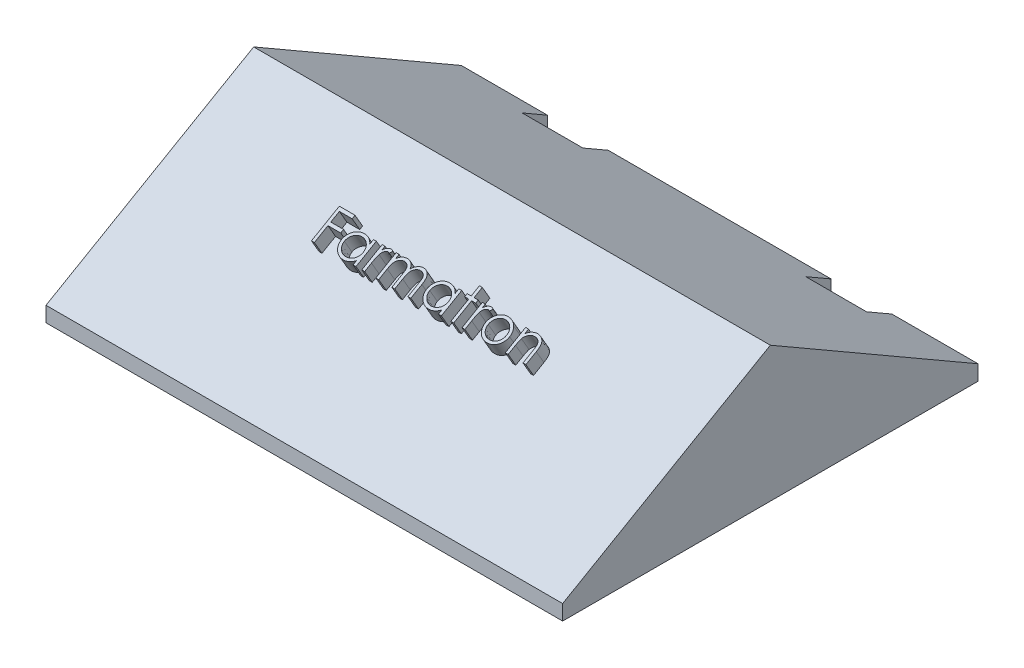
SolidWorks part; units mm, degrees
ref_plane "Front" through (0, 0, 0) normal (0, 0, 1) x (1, 0, 0)
ref_plane "Top" through (0, 0, 0) normal (0, 1, 0) x (1, 0, 0)
ref_plane "Right" through (0, 0, 0) normal (1, 0, 0) x (0, 0, -1)
sketch "Sketch1" plane through (0, 0, 0) normal (0, 1, 0) x (1, 0, 0)
  line L1 (-51, -41) -> (51, -41)
  line L2 (-51, -41) -> (-51, 41)
  line L3 (-51, 41) -> (51, 41)
  line L4 (51, -41) -> (51, 41)
  line L5 (-51, -41) -> (51, 41) construction
  line L6 (-51, 41) -> (51, -41) construction
  point P0 (0, 0)
  dimension "D1" = 102
  dimension "D2" = 82
extrude "Boss-Extrude1" add sketch "Sketch1" along normal blind 3
sketch "Sketch2" plane through (0, 0, 0) normal (0, -1, 0) x (1, 0, 0)
  line L1 (-45.5, -35.5) -> (45.5, -35.5)
  line L2 (-45.5, -35.5) -> (-45.5, 35.5)
  line L3 (-45.5, 35.5) -> (45.5, 35.5)
  line L4 (45.5, -35.5) -> (45.5, 35.5)
  line L5 (-45.5, -35.5) -> (45.5, 35.5) construction
  line L6 (-45.5, 35.5) -> (45.5, -35.5) construction
  point P0 (0, 0)
  dimension "D1" = 91
  dimension "D2" = 71
extrude "Boss-Extrude2" add sketch "Sketch2" along normal blind 3
sketch "Sketch5" plane through (-51, 0, 0) normal (-1, 0, 0) x (0, 0, 1)
  line L0 (41, 3) -> (-36.5346, 47.7646)
  line L1 (-41, 3) -> (41, 3) construction
  line L2 (-41, 3) -> (6.5786, 30.4695)
  line L3 (-41, 3) -> (41, 3)
  line M5 (41, 3) -> (-41, 3)
  dimension "D1" = 30
  dimension "D2" = 30
extrude "Boss-Extrude4" add sketch "Sketch5" against normal blind 102 contours L2 L0 M5
sketch "Sketch7" plane through (0, 0, 0) normal (0, 1, 0) x (-1, 0, 0)
  line L2 (-34, -43) -> (-22, -43)
  line L3 (-34, -43) -> (-34, -36)
  line L4 (-34, -36) -> (-22, -36)
  line L5 (-22, -43) -> (-22, -36)
  line L6 (-34, -43) -> (-22, -36) construction
  line L7 (0, 0) -> (0, -106.1557) construction
  line L8 (-34, -36) -> (-22, -43) construction
  line L9 (22, -43) -> (34, -43)
  line L10 (22, -43) -> (22, -36)
  line L11 (22, -36) -> (34, -36)
  line L12 (34, -43) -> (34, -36)
  line L13 (22, -43) -> (34, -36) construction
  line L14 (-61.1846, -39.5) -> (66.7555, -39.5) construction
  line L15 (-51, -41) -> (51, -41) construction
  line L16 (22, -36) -> (34, -43) construction
  point P0 (-28, -39.5)
  point P5 (28, -39.5)
  dimension "D1" = 12
  dimension "D2" = 7
  dimension "D3" = 28
  dimension "D5" = 7
  dimension "D6" = 1.5
  dimension "D4" = 12
  dimension "D7" = 28
sketch "Sketch6" plane through (0, 20.0035, 11.549) normal (0, 0.866, 0.5) x (1, 0, 0)
  text T0 "         Farmatron"
  point P0 (0, 0)
extrude "Boss-Extrude5" add sketch "Sketch6" along normal blind 3
extrude "Cut-Extrude1" cut sketch "Sketch7" against normal blind 10 and the other way up to next
